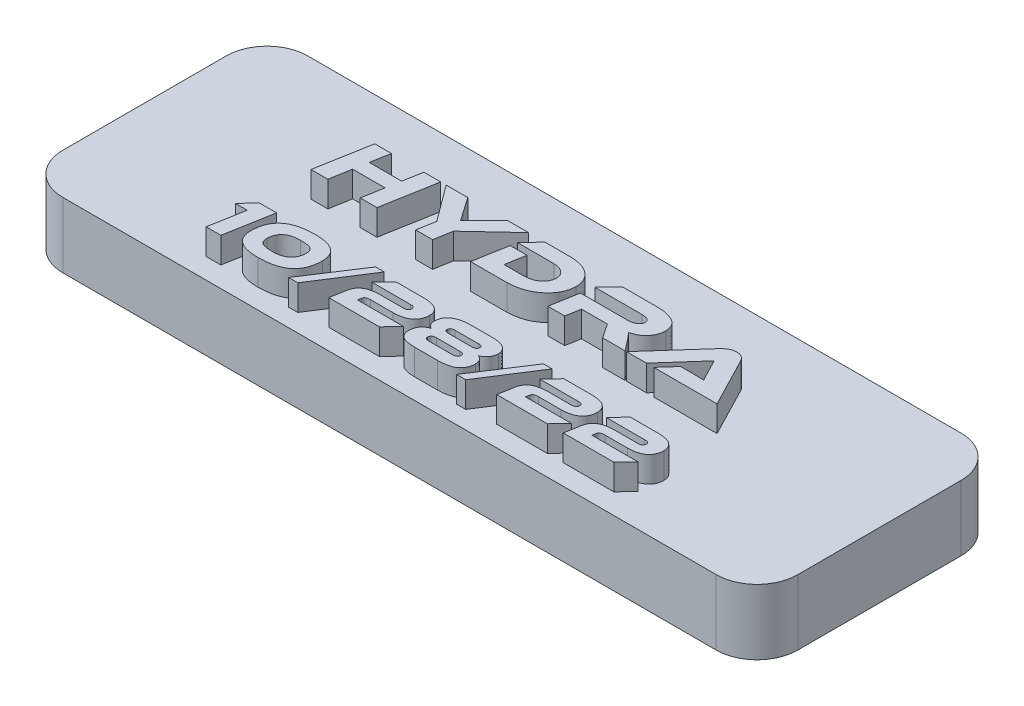
SolidWorks part; units mm, degrees
ref_plane "Front Plane" through (0, 0, 0) normal (0, 0, 1) x (1, 0, 0)
ref_plane "Top Plane" through (0, 0, 0) normal (0, 1, 0) x (1, 0, 0)
ref_plane "Right Plane" through (0, 0, 0) normal (1, 0, 0) x (0, 0, -1)
sketch "Sketch1" plane through (0, 0, 0) normal (0, 1, 0) x (1, 0, 0)
  line L1 (-28.575, 9.525) -> (28.575, 9.525)
  line L2 (-28.575, 9.525) -> (-28.575, -9.525)
  line L3 (-28.575, -9.525) -> (28.575, -9.525)
  line L4 (28.575, 9.525) -> (28.575, -9.525)
  line L5 (-28.575, 9.525) -> (28.575, -9.525) construction
  line L6 (-28.575, -9.525) -> (28.575, 9.525) construction
  point P0 (0, 0)
  dimension "D1" = 57.15
  dimension "D2" = 19.05
extrude "Boss-Extrude1" add sketch "Sketch1" along normal up to surface (5.08 mm away)
fillet "Fillet1" radius 3.175 4 edges at (-28.575, 2.54, 9.525) (-28.575, 2.54, -9.525) (28.575, 2.54, 9.525) (28.575, 2.54, -9.525)
sketch "Sketch3" plane through (0, 5.08, 0) normal (0, 1, 0) x (1, 0, 0)
  line L0 (28.575, -7.9375) -> (-28.575, -7.9375) construction
  line L1 (28.575, -6.35) -> (28.575, 6.35) construction
  line L2 (-28.575, 6.35) -> (-28.575, -6.35) construction
  line L3 (28.575, 0) -> (-28.575, 0) construction
  line L5 (-25.4, -9.525) -> (25.4, -9.525) construction
  line L6 (25.4, 9.525) -> (-25.4, 9.525) construction
  text T0 "hydra\r\n" font "Ethnocentric Rg" height in points 16
  text T1 "10/28/22" font "Ethnocentric Rg" height in points 14
  point P8 (-28.575, 0)
  dimension "D1" = 1.5875
extrude "Boss-Extrude2" add sketch "Sketch3" along normal blind 2
sketch "Sketch4" plane through (0, 0, 0) normal (0, -1, 0) x (1, 0, 0)
  line L0 (25.4, 0) -> (-25.4, 0) construction
  circle A0 centre (-25.4, 0) radius 0.9
  circle A1 centre (25.4, 0) radius 0.9
  point P3 (0, 0)
  dimension "D2" = 1.8
  dimension "D1" = 50.8
extrude "Cut-Extrude1" cut sketch "Sketch4" against normal blind 4
